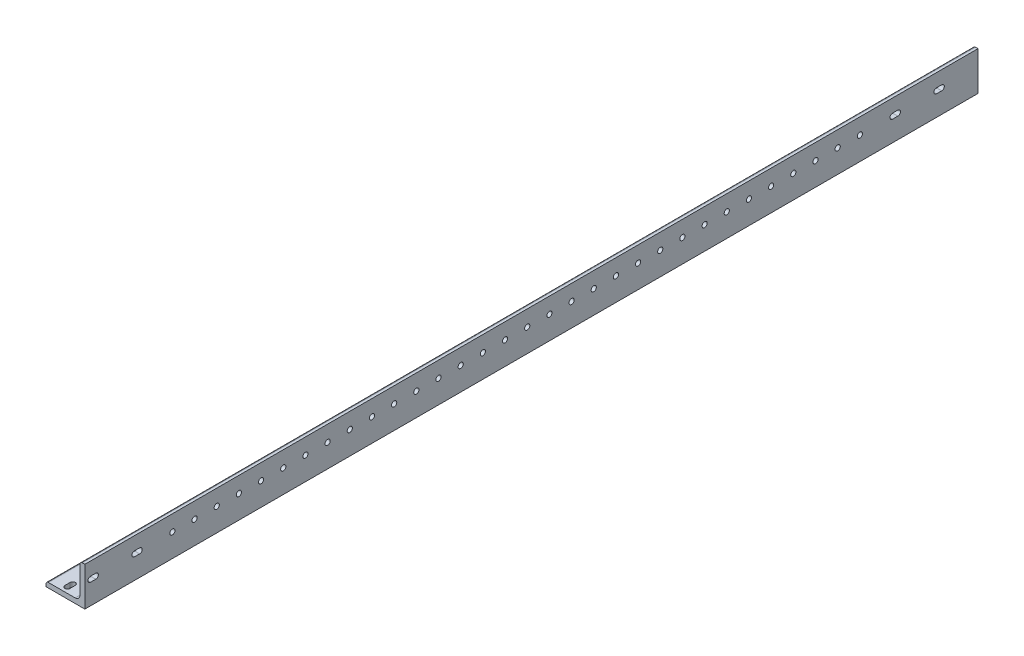
SolidWorks part; units mm, degrees
ref_plane "Front Plane" through (0, 0, 0) normal (0, 0, 1) x (1, 0, 0)
ref_plane "Top Plane" through (0, 0, 0) normal (0, 1, 0) x (1, 0, 0)
ref_plane "Right Plane" through (0, 0, 0) normal (1, 0, 0) x (0, 0, -1)
sketch "Sketch0" plane through (0, 0, 0) normal (0, 0, 1) x (1, 0, 0)
  line L0 (-12.7, -12.7) -> (12.7, -12.7)
  line L1 (12.7, -12.7) -> (12.7, 12.7)
  line L2 (12.7, 0) -> (0, 0) construction
  line L3 (0, 0) -> (0, -12.7) construction
  line L4 (9.525, -6.35) -> (9.525, 12.7) construction
  line L5 (6.35, -9.525) -> (-12.7, -9.525) construction
  arc A0 (9.525, -6.35) -> (6.35, -9.525) centre (6.35, -6.35) cw
  point P3 (8.5951, -8.5951)
  dimension "Inside Corner Radius" = 3.175
  dimension "Outside Height" = 25.4
  dimension "Inside Height" = 22.225
  dimension "Inside Width" = 22.225
  dimension "Wall Thickness" = 3.175
  dimension "D1" = 3.175
  dimension "Outside Width" = 25.4
sketch "Sketch1" plane through (0, 0, 0) normal (1, 0, 0) x (0, 0, -1)
  line L0 (609.6, 0) -> (-609.6, 0)
  point P4 (0, 0)
  dimension "Length" = 1219.2
sketch "Sketch2" plane through (0, 0, 0) normal (0, 0, 1) x (1, 0, 0)
  line L0 (-12.7, -12.7) -> (12.7, -12.7)
  line L1 (12.7, -12.7) -> (12.7, 12.7)
  line L2 (12.7, 12.7) -> (9.525, 12.7) construction
  line L3 (9.525, 11.1125) -> (9.525, -6.35)
  line L4 (6.35, -9.525) -> (-11.1125, -9.525)
  line L5 (-12.7, -12.7) -> (-12.7, -9.525) construction
  line L6 (11.1125, 12.7) -> (12.7, 12.7)
  line L7 (-12.7, -11.1125) -> (-12.7, -12.7)
  line L8 (12.7, 0) -> (0, 0) construction
  line L9 (0, 0) -> (0, -12.7) construction
  arc A0 (9.525, 11.1125) -> (11.1125, 12.7) centre (11.1125, 11.1125) cw
  arc A1 (-12.7, -11.1125) -> (-11.1125, -9.525) centre (-11.1125, -11.1125) cw
  arc A2 (9.525, -6.35) -> (6.35, -9.525) centre (6.35, -6.35) cw
  dimension "Inside Radius" = 3.175
  dimension "Height" = 25.4
  dimension "Width" = 25.4
  dimension "Thickness" = 3.175
extrude "Boss-Extrude1" add sketch "Sketch2" along normal mid plane 1219.2
sketch "Break Locations" plane through (0, 0, 0) normal (1, 0, 0) x (0, 0, -1)
  line L0 (-583.692, 0) -> (583.692, 0)
  line L1 (-609.6, -12.7) -> (-609.6, 12.7) construction
  line L2 (609.6, -12.7) -> (609.6, 12.7) construction
  point P0 (-588.01, 0)
  point P1 (588.01, 0)
  point P10 (0, 0)
  point P11 (583.692, 0)
  point P13 (-583.692, 0)
  dimension "D1" = 21.59
  dimension "D2" = 21.59
  dimension "D3" = 25.908
sketch "Sketch3" plane through (12.7, 0, 0) normal (1, 0, 0) x (0, 0, -1)
  line L0 (-609.6, -12.7) -> (609.6, -12.7) construction
  line L1 (609.6, 12.7) -> (-25.6, 12.7)
  line L2 (609.6, 12.7) -> (609.6, -12.7)
  line L3 (609.6, -12.7) -> (-25.6, -12.7)
  line L4 (-25.6, 12.7) -> (-25.6, -12.7)
  line L5 (-609.6, -12.7) -> (-609.6, 12.7) construction
  dimension "D1" = 584
extrude "Cut-Extrude2" cut sketch "Sketch3" against normal blind 30.48
sketch "Sketch4" plane through (0, -9.525, 0) normal (0, 1, 0) x (1, 0, 0)
  line L0 (-11.1125, -92.4325) -> (6.35, -92.4325) construction
  line L1 (-11.1125, -609.6) -> (-11.1125, -25.6) construction
  line L2 (3.9675, -92.4325) -> (-8.7325, -92.4325) construction
  line L3 (6.35, -609.6) -> (6.35, -25.6) construction
  line L4 (-2.3812, -92.4325) -> (-2.3812, -562.7675) construction
  line L6 (-11.1125, -562.7675) -> (6.35, -562.7675) construction
  line L7 (-2.3812, -552.35) -> (-2.3812, -562.7675)
  line L8 (-2.3813, -102.85) -> (-2.3812, -92.4325)
  line L9 (-12.7, -635) -> (12.7, -635) construction
  circle A0 centre (-2.3812, -552.35) radius 1.7
  circle A1 centre (-2.3813, -537.85) radius 1.7
  circle A2 centre (-2.3813, -523.35) radius 1.7
  circle A3 centre (-2.3813, -508.85) radius 1.7
  circle A4 centre (-2.3813, -494.35) radius 1.7
  circle A5 centre (-2.3813, -479.85) radius 1.7
  circle A6 centre (-2.3813, -465.35) radius 1.7
  circle A7 centre (-2.3813, -450.85) radius 1.7
  circle A8 centre (-2.3813, -436.35) radius 1.7
  circle A9 centre (-2.3813, -421.85) radius 1.7
  circle A10 centre (-2.3813, -407.35) radius 1.7
  circle A11 centre (-2.3813, -392.85) radius 1.7
  circle A12 centre (-2.3813, -378.35) radius 1.7
  circle A13 centre (-2.3813, -363.85) radius 1.7
  circle A14 centre (-2.3813, -349.35) radius 1.7
  circle A15 centre (-2.3813, -334.85) radius 1.7
  circle A16 centre (-2.3813, -320.35) radius 1.7
  circle A17 centre (-2.3813, -305.85) radius 1.7
  circle A18 centre (-2.3813, -291.35) radius 1.7
  circle A19 centre (-2.3813, -276.85) radius 1.7
  circle A20 centre (-2.3813, -262.35) radius 1.7
  circle A21 centre (-2.3813, -247.85) radius 1.7
  circle A22 centre (-2.3813, -233.35) radius 1.7
  circle A23 centre (-2.3813, -218.85) radius 1.7
  circle A24 centre (-2.3813, -204.35) radius 1.7
  circle A25 centre (-2.3813, -189.85) radius 1.7
  circle A26 centre (-2.3813, -175.35) radius 1.7
  circle A27 centre (-2.3813, -160.85) radius 1.7
  circle A28 centre (-2.3813, -146.35) radius 1.7
  circle A29 centre (-2.3813, -131.85) radius 1.7
  circle A30 centre (-2.3813, -117.35) radius 1.7
  circle A31 centre (-2.3813, -102.85) radius 1.7
  dimension "D1" = 3.4
  dimension "D3" = 14.5
  dimension "D4" = 72.2325
  dimension "D2" = 32
extrude "Cut-Extrude4" cut sketch "Sketch4" against normal through all contours A0 | A1 | A2 | A3 | A4 | A5 | A6 | A7 | A8 | A9 | A10 | A11 | A12 | A13 | A14 | A15 | A16 | A17 | A18 | A19 | A20 | A21 | A22 | A23 | A24 | A25 | A26 | A27 | A28 | A29 | A30 | A31
sketch "Sketch7" plane through (9.525, 0, 0) normal (-1, 0, 0) x (0, 0, 1)
  line L0 (92.4325, 11.1125) -> (92.4325, -6.35) construction
  line L1 (562.7675, 11.1125) -> (562.7675, -6.35) construction
  line L2 (609.6, 11.1125) -> (25.6, 11.1125) construction
  line L4 (609.6, -6.35) -> (25.6, -6.35) construction
  line L5 (92.4325, 2.3812) -> (562.7675, 2.3812) construction
  line L7 (102.85, 2.3812) -> (92.4325, 2.3812)
  line L8 (552.35, 2.3812) -> (562.7675, 2.3812)
  line L9 (628.65, -12.7) -> (628.65, 147.3) construction
  line L10 (20.2, -12.7) -> (20.2, 147.3) construction
  circle A0 centre (552.35, 2.3812) radius 1.7
  circle A1 centre (537.85, 2.3812) radius 1.7
  circle A2 centre (523.35, 2.3812) radius 1.7
  circle A3 centre (508.85, 2.3812) radius 1.7
  circle A4 centre (494.35, 2.3812) radius 1.7
  circle A5 centre (479.85, 2.3812) radius 1.7
  circle A6 centre (465.35, 2.3812) radius 1.7
  circle A7 centre (450.85, 2.3812) radius 1.7
  circle A8 centre (436.35, 2.3812) radius 1.7
  circle A9 centre (421.85, 2.3812) radius 1.7
  circle A10 centre (407.35, 2.3812) radius 1.7
  circle A11 centre (392.85, 2.3812) radius 1.7
  circle A12 centre (378.35, 2.3812) radius 1.7
  circle A13 centre (363.85, 2.3812) radius 1.7
  circle A14 centre (349.35, 2.3812) radius 1.7
  circle A15 centre (334.85, 2.3812) radius 1.7
  circle A16 centre (320.35, 2.3812) radius 1.7
  circle A17 centre (305.85, 2.3812) radius 1.7
  circle A18 centre (291.35, 2.3812) radius 1.7
  circle A19 centre (276.85, 2.3812) radius 1.7
  circle A20 centre (262.35, 2.3812) radius 1.7
  circle A21 centre (247.85, 2.3812) radius 1.7
  circle A22 centre (233.35, 2.3812) radius 1.7
  circle A23 centre (218.85, 2.3812) radius 1.7
  circle A24 centre (204.35, 2.3812) radius 1.7
  circle A25 centre (189.85, 2.3812) radius 1.7
  circle A26 centre (175.35, 2.3812) radius 1.7
  circle A27 centre (160.85, 2.3812) radius 1.7
  circle A28 centre (146.35, 2.3812) radius 1.7
  circle A29 centre (131.85, 2.3812) radius 1.7
  circle A30 centre (117.35, 2.3812) radius 1.7
  circle A31 centre (102.85, 2.3812) radius 1.7
  dimension "D1" = 3.4
  dimension "D3" = 14.5
  dimension "D4" = 65.8825
  dimension "D5" = 72.2325
  dimension "D2" = 32
extrude "Cut-Extrude6" cut sketch "Sketch7" against normal through all
sketch "Sketch8" plane through (9.525, 0, 0) normal (-1, 0, 0) x (0, 0, 1)
  line L0 (49.3305, 2.3825) -> (52.7305, 2.3825) construction
  line L1 (49.3305, 4.0825) -> (52.7305, 4.0825)
  line L2 (49.3305, 0.6825) -> (52.7305, 0.6825)
  line L3 (78.0325, 2.3825) -> (81.4325, 2.3825) construction
  line L4 (78.0325, 4.0825) -> (81.4325, 4.0825)
  line L5 (78.0325, 0.6825) -> (81.4325, 0.6825)
  line L6 (573.7675, 2.3825) -> (577.1675, 2.3825) construction
  line L7 (573.7675, 4.0825) -> (577.1675, 4.0825)
  line L8 (573.7675, 0.6825) -> (577.1675, 0.6825)
  line L9 (602.4695, 2.3825) -> (605.8695, 2.3825) construction
  line L10 (602.4695, 4.0825) -> (605.8695, 4.0825)
  line L11 (602.4695, 0.6825) -> (605.8695, 0.6825)
  circle A0 centre (79.7325, 2.3825) radius 1.7 construction
  circle A1 centre (51.0305, 2.3825) radius 1.7 construction
  circle A2 centre (575.4675, 2.3825) radius 1.7 construction
  circle A3 centre (604.1695, 2.3825) radius 1.7 construction
  arc A4 (49.3305, 4.0825) -> (49.3305, 0.6825) centre (49.3305, 2.3825) ccw
  arc A5 (52.7305, 0.6825) -> (52.7305, 4.0825) centre (52.7305, 2.3825) ccw
  arc A6 (78.0325, 4.0825) -> (78.0325, 0.6825) centre (78.0325, 2.3825) ccw
  arc A7 (81.4325, 0.6825) -> (81.4325, 4.0825) centre (81.4325, 2.3825) ccw
  arc A8 (573.7675, 4.0825) -> (573.7675, 0.6825) centre (573.7675, 2.3825) ccw
  arc A9 (577.1675, 0.6825) -> (577.1675, 4.0825) centre (577.1675, 2.3825) ccw
  arc A10 (602.4695, 4.0825) -> (602.4695, 0.6825) centre (602.4695, 2.3825) ccw
  arc A11 (605.8695, 0.6825) -> (605.8695, 4.0825) centre (605.8695, 2.3825) ccw
  point P14 (51.0305, 2.3825)
  point P21 (79.7325, 2.3825)
  point P27 (575.4675, 2.3825)
  point P35 (604.1695, 2.3825)
  dimension "D1" = 3.4
extrude "Cut-Extrude7" cut sketch "Sketch8" against normal through all
sketch "Sketch9" plane through (0, -9.525, 0) normal (0, 1, 0) x (1, 0, 0)
  line L0 (-2.3825, -605.8695) -> (-2.3825, -602.4695) construction
  line L1 (-4.0825, -605.8695) -> (-4.0825, -602.4695)
  line L2 (-0.6825, -605.8695) -> (-0.6825, -602.4695)
  line L3 (-2.3825, -577.1675) -> (-2.3825, -573.7675) construction
  line L4 (-4.0825, -577.1675) -> (-4.0825, -573.7675)
  line L5 (-0.6825, -577.1675) -> (-0.6825, -573.7675)
  line L6 (-2.3825, -81.4325) -> (-2.3825, -78.0325) construction
  line L7 (-4.0825, -81.4325) -> (-4.0825, -78.0325)
  line L8 (-0.6825, -81.4325) -> (-0.6825, -78.0325)
  line L9 (-2.3825, -52.7305) -> (-2.3825, -49.3305) construction
  line L10 (-4.0825, -52.7305) -> (-4.0825, -49.3305)
  line L11 (-0.6825, -52.7305) -> (-0.6825, -49.3305)
  circle A0 centre (-2.3825, -604.1695) radius 1.7 construction
  circle A1 centre (-2.3825, -575.4675) radius 1.7 construction
  circle A2 centre (-2.3825, -51.0305) radius 1.7 construction
  circle A3 centre (-2.3825, -79.7325) radius 1.7 construction
  arc A4 (-4.0825, -605.8695) -> (-0.6825, -605.8695) centre (-2.3825, -605.8695) ccw
  arc A5 (-0.6825, -602.4695) -> (-4.0825, -602.4695) centre (-2.3825, -602.4695) ccw
  arc A6 (-4.0825, -577.1675) -> (-0.6825, -577.1675) centre (-2.3825, -577.1675) ccw
  arc A7 (-0.6825, -573.7675) -> (-4.0825, -573.7675) centre (-2.3825, -573.7675) ccw
  arc A8 (-4.0825, -81.4325) -> (-0.6825, -81.4325) centre (-2.3825, -81.4325) ccw
  arc A9 (-0.6825, -78.0325) -> (-4.0825, -78.0325) centre (-2.3825, -78.0325) ccw
  arc A10 (-4.0825, -52.7305) -> (-0.6825, -52.7305) centre (-2.3825, -52.7305) ccw
  arc A11 (-0.6825, -49.3305) -> (-4.0825, -49.3305) centre (-2.3825, -49.3305) ccw
  point P14 (-2.3825, -604.1695)
  point P21 (-2.3825, -575.4675)
  point P27 (-2.3825, -79.7325)
  point P34 (-2.3825, -51.0305)
  dimension "D1" = 3.4
extrude "Cut-Extrude8" cut sketch "Sketch9" against normal through all contours L2 A5 L1 A4 | L5 A7 L4 A6 | L8 A8 L7 A9 | L11 A11 L10 A10
equation "\"D1@Break Locations\" = .85 * \"Height@Sketch2\""
equation "\"D2@Break Locations\"=\"D1@Break Locations\""
equation "\"Thickness@Sketch2\" = \"Wall Thickness@Sketch0\""
equation "\"Height@Sketch2\" = \"Outside Height@Sketch0\""
equation "\"Width@Sketch2\" = \"Outside Width@Sketch0\""
equation "\"Inside Radius@Sketch2\" = \"Inside Corner Radius@Sketch0\""
equation "\"Length@Boss-Extrude1\" = \"Length@Sketch1\""
equation "\"D3@Break Locations\"=\"D2@Break Locations\"*1.2"
equation "\"D1@Sketch0\"=\"Wall Thickness@Sketch0\""
